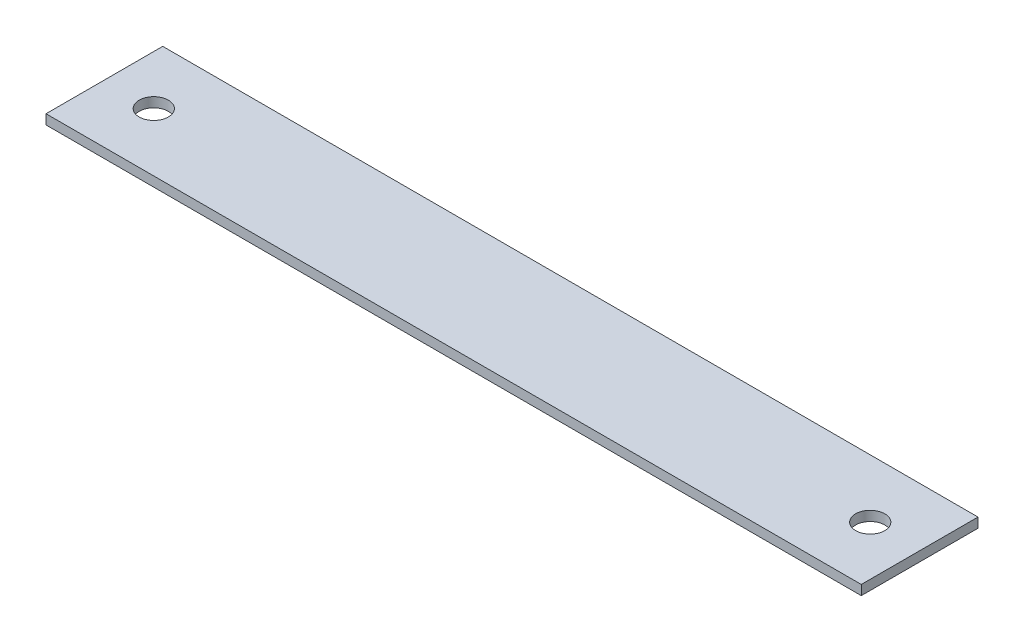
SolidWorks part; units mm, degrees
ref_plane "Front Plane" through (0, 0, 0) normal (0, 0, 1) x (1, 0, 0)
ref_plane "Top Plane" through (0, 0, 0) normal (0, 1, 0) x (1, 0, 0)
ref_plane "Right Plane" through (0, 0, 0) normal (1, 0, 0) x (0, 0, -1)
sketch "Sketch1" plane through (0, 0, 0) normal (0, 1, 0) x (1, 0, 0)
  line L1 (0, 0) -> (419.1, 0)
  line L2 (0, 0) -> (0, 60)
  line L3 (0, 60) -> (419.1, 60)
  line L4 (419.1, 0) -> (419.1, 60)
  circle A0 centre (25.4, 30) radius 7.5
  circle A1 centre (393.7, 30) radius 7.5
  point P10 (419.1, 30)
  dimension "D3" = 15
  dimension "D6" = 15
  dimension "D1" = 419.1
  dimension "D2" = 60
  dimension "D4" = 25.4
  dimension "D5" = 25.4
extrude "Boss-Extrude1" add sketch "Sketch1" along normal blind 5 contours L1 L4 L3 L2 A1 A0
